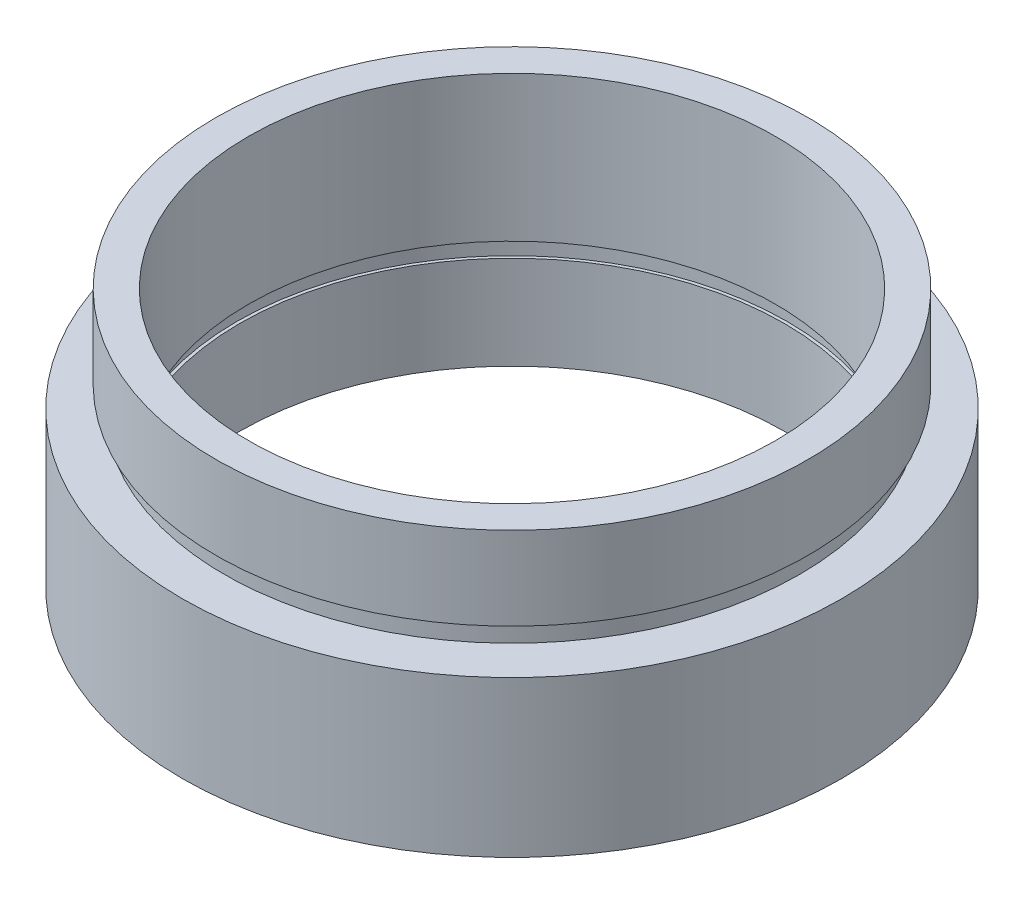
SolidWorks part; units mm, degrees
ref_plane "前视基准面" through (0, 0, 0) normal (0, 0, 1) x (1, 0, 0)
ref_plane "上视基准面" through (0, 0, 0) normal (0, 1, 0) x (1, 0, 0)
ref_plane "右视基准面" through (0, 0, 0) normal (1, 0, 0) x (0, 0, -1)
sketch "草图1" plane through (0, 0, 0) normal (0, 0, 1) x (1, 0, 0)
  line L0 (0, 16.886) -> (0, -24.4878) construction
  line L1 (13.1, 0) -> (13.1, 4.5)
  line L2 (13.25, 4.5) -> (13.25, 5.5)
  line L3 (13.1, 4.5) -> (13.25, 4.5)
  line L4 (12.69, 12.5) -> (12.69, 5.5)
  line L5 (14.26, 12.5) -> (14.26, 8.5)
  line L6 (14.26, 8.5) -> (13.85, 8.5)
  line L7 (13.85, 8.5) -> (13.85, 7.5)
  line L8 (13.85, 7.5) -> (15.875, 7.5)
  line L9 (15.875, 7.5) -> (15.875, 0)
  line L10 (15.875, 0) -> (13.1, 0)
  line L11 (12.69, 12.5) -> (14.26, 12.5)
  line L12 (12.69, 5.5) -> (13.25, 5.5)
  line L13 (0, 0) -> (3.4668, 0) construction
  point P4 (14.4875, 0)
  dimension "D1" = 13.1
  dimension "D2" = 14.26
  dimension "D3" = 13.85
  dimension "D4" = 13.25
  dimension "D5" = 1
  dimension "D6" = 15.875
  dimension "D7" = 12.69
  dimension "D8" = 7.5
  dimension "D9" = 1
  dimension "D10" = 12.5
  dimension "D11" = 7
revolve "旋转1" add sketch "草图1" angle 360 about L0
cosmetic thread "装饰螺纹线1"
cosmetic thread "装饰螺纹线2"
cosmetic thread "装饰螺纹线3"
